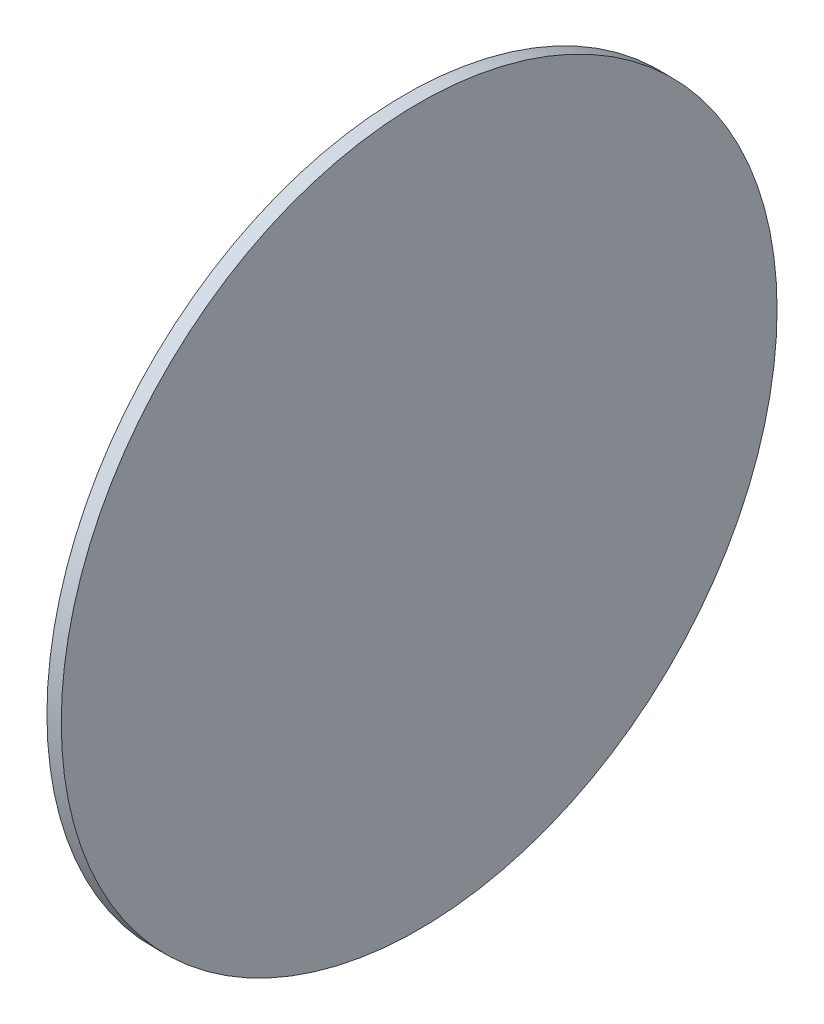
SolidWorks part; units mm, degrees
ref_plane "Front Plane" through (0, 0, 0) normal (0, 0, 1) x (1, 0, 0)
ref_plane "Top Plane" through (0, 0, 0) normal (0, 1, 0) x (1, 0, 0)
ref_plane "Right Plane" through (0, 0, 0) normal (1, 0, 0) x (0, 0, -1)
sketch "Sketch1" plane through (0, 0, 0) normal (1, 0, 0) x (0, 0, -1)
  circle A0 centre (0, 0) radius 250
  dimension "D1" = 500
extrude "Boss-Extrude1" add sketch "Sketch1" along normal blind 10
